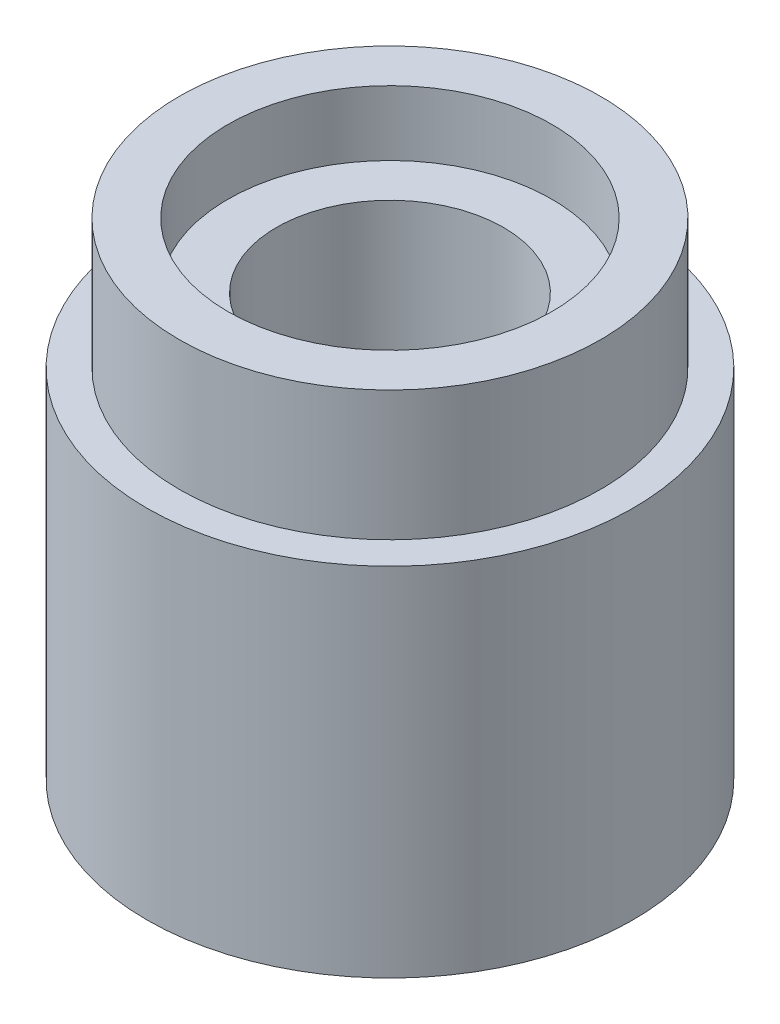
SolidWorks part; units mm, degrees
ref_plane "Front Plane" through (0, 0, 0) normal (0, 0, 1) x (1, 0, 0)
ref_plane "Top Plane" through (0, 0, 0) normal (0, 1, 0) x (1, 0, 0)
ref_plane "Right Plane" through (0, 0, 0) normal (1, 0, 0) x (0, 0, -1)
sketch "Sketch1" plane through (0, 0, 0) normal (0, 1, 0) x (1, 0, 0)
  circle A0 centre (0, 0) radius 3.75
extrude "Boss-Extrude1" add sketch "Sketch1" along normal blind 7.5
sketch "Sketch2" plane through (0, 7.5, 0) normal (0, 1, 0) x (1, 0, 0)
  circle A0 centre (0, 0) radius 2.5
  circle A1 centre (0, 0) radius 3.75
sketch "Sketch3" plane through (0, 7.5, 0) normal (0, 1, 0) x (1, 0, 0)
  circle A0 centre (0, 0) radius 1.75
sketch "Sketch4" plane through (0, 7.5, 0) normal (0, 1, 0) x (1, 0, 0)
  circle A0 centre (0, 0) radius 3.25
  circle A1 centre (0, 0) radius 3.75
extrude "Cut-Extrude1" cut sketch "Sketch4" against normal blind 2
sketch "Sketch5" plane through (0, 7.5, 0) normal (0, 1, 0) x (1, 0, 0)
  circle A0 centre (0, 0) radius 1.75
extrude "Cut-Extrude2" cut sketch "Sketch5" against normal blind 7
sketch "Sketch6" plane through (0, 7.5, 0) normal (0, 1, 0) x (1, 0, 0)
  circle A0 centre (0, 0) radius 2.5
extrude "Cut-Extrude3" cut sketch "Sketch6" against normal blind 1
